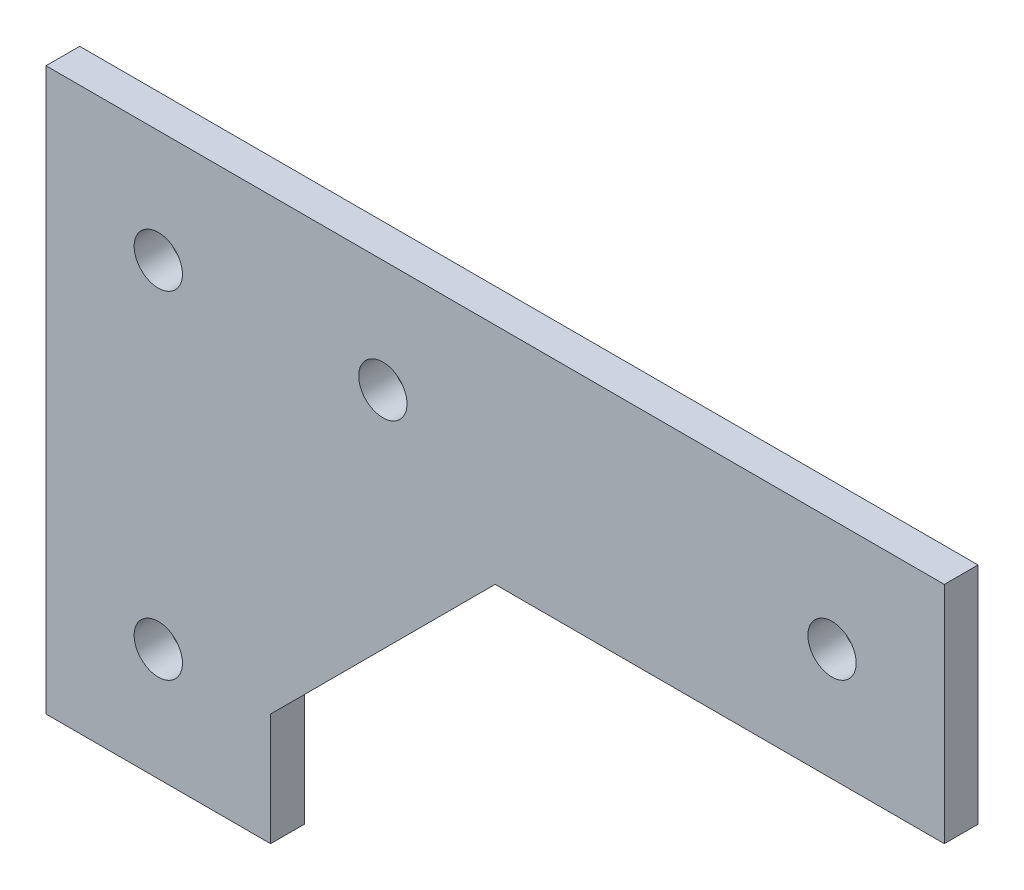
SolidWorks part; units mm, degrees
material "Thornel Mat VMA"
ref_plane "Front Plane" through (0, 0, 0) normal (0, 0, 1) x (1, 0, 0)
ref_plane "Top Plane" through (0, 0, 0) normal (0, 1, 0) x (1, 0, 0)
ref_plane "Right Plane" through (0, 0, 0) normal (1, 0, 0) x (0, 0, -1)
sketch "Sketch1" plane through (0, 0, 0) normal (0, 0, 1) x (1, 0, 0)
  line L0 (52.497, 165) -> (-27.503, 165)
  line L1 (-7.503, 165) -> (592.497, 165) construction
  line L2 (-27.503, 20) -> (-27.503, 260) construction
  line L3 (-27.503, 165) -> (-27.503, 115)
  line L4 (-27.503, 115) -> (-7.503, 115)
  line L5 (-7.503, 145) -> (-7.503, 20) construction
  line L6 (-7.503, 115) -> (-7.503, 125)
  line L7 (592.497, 145) -> (-7.503, 145) construction
  line L8 (12.497, 145) -> (52.497, 145)
  line L9 (35.4974, 145) -> (22.4974, 145) construction
  line L10 (52.497, 145) -> (52.497, 165)
  line L11 (-7.503, 125) -> (12.497, 145)
  line L12 (-17.503, 115) -> (-17.503, 165) construction
  line L13 (52.497, 155) -> (-27.503, 155) construction
  line L14 (-7.503, 260) -> (-7.503, 165) construction
  circle A0 centre (2.497, 155) radius 2.15
  circle A1 centre (42.497, 155) radius 2.15
  circle A2 centre (-17.503, 125) radius 2.15
  circle A3 centre (-17.503, 155) radius 2.15
  point P11 (-7.503, 145)
  dimension "D1" = 4.3
  dimension "D2" = 10
  dimension "D4" = 10
  dimension "D5" = 10
  dimension "D6" = 40
  dimension "D7" = 30
extrude "Extrude1" add sketch "Sketch1" along normal blind 3
